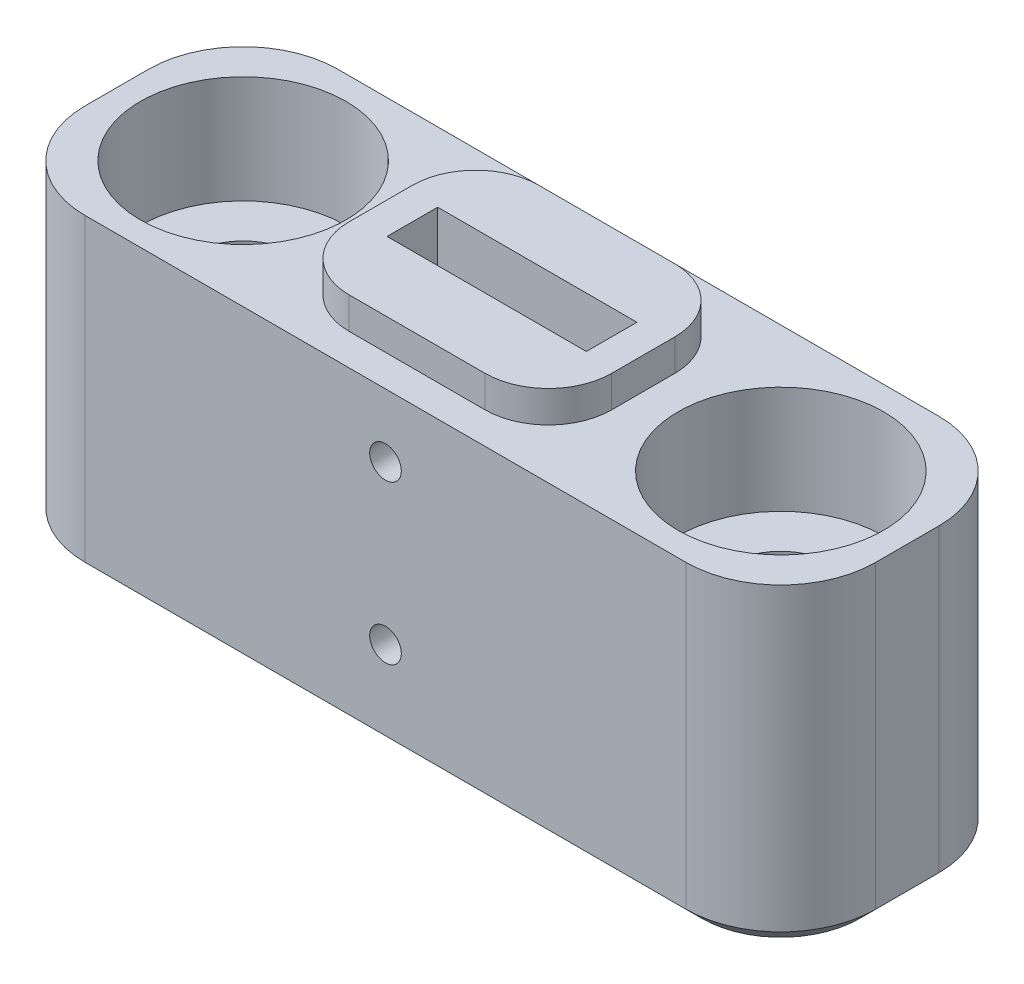
SolidWorks part; units mm, degrees
material "PUR"
ref_plane "Ebene vorne" through (0, 0, 0) normal (0, 0, 1) x (1, 0, 0)
ref_plane "Ebene oben" through (0, 0, 0) normal (0, 1, 0) x (1, 0, 0)
ref_plane "Ebene rechts" through (0, 0, 0) normal (1, 0, 0) x (0, 0, -1)
sketch "Skizze1" plane through (0, 0, 0) normal (0, 0, 1) x (1, 0, 0)
  line L1 (12.5, -5) -> (-12.5, -5)
  line L2 (12.5, -5) -> (12.5, 5)
  line L3 (12.5, 5) -> (-12.5, 5)
  line L4 (-12.5, -5) -> (-12.5, 5)
  line L5 (12.5, -5) -> (-12.5, 5) construction
  line L6 (12.5, 5) -> (-12.5, -5) construction
  point P0 (0, 0)
  dimension "D1" = 10
  dimension "D2" = 25
extrude "Aufsatz-Linear austragen1" add sketch "Skizze1" along normal mid plane 8
hole_wizard "Stirnsenkung für M3 Zylinderschraube mit Innensechskant1" positions "Skizze2" profile "Skizze3" counterbore size "M3" standard "ISO" end condition through all
sketch "Skizze2" plane through (0, 5, 0) normal (0, 1, 0) x (1, 0, 0)
  line L0 (8.5, 0) -> (0, 0) construction
  line L1 (0, 0) -> (-8.5, 0) construction
  point P0 (-8.5, 0)
  point P2 (8.5, 0)
  dimension "D1" = 17
sketch "Skizze3" plane through (-8.5, 5, 0) normal (1, 0, 0) x (0, 0, 1)
  line L0 (0, 0) -> (0, 10)
  line L1 (0, 10) -> (1.7, 10)
  line L3 (1.7, 10) -> (1.7, 3.4)
  line L4 (1.7, 3.4) -> (3.25, 3.4)
  line L5 (3.25, 3.4) -> (3.25, 0)
  line L7 (3.25, 0) -> (0, 0)
  line L11 (0, -6.35) -> (0, 107.95) construction
  dimension "Bohrerdurchmesser" = 3.4
  dimension "Bohrungstiefe" = 10
  dimension "Senkdurchmesser2" = 6.5
  dimension "Senktiefe2" = 3.4
fillet "Verrundung1" radius 3 4 edges at (12.5, 0, -4) (12.5, 0, 4) (-12.5, 0, -4) (-12.5, 0, 4)
sketch "Skizze4" plane through (0, 5, 0) normal (0, 1, 0) x (1, 0, 0)
  line L1 (3.15, -0.8) -> (-3.15, -0.8)
  line L2 (3.15, -0.8) -> (3.15, 0.8)
  line L3 (3.15, 0.8) -> (-3.15, 0.8)
  line L4 (-3.15, -0.8) -> (-3.15, 0.8)
  line L5 (3.15, -0.8) -> (-3.15, 0.8) construction
  line L6 (3.15, 0.8) -> (-3.15, -0.8) construction
  point P0 (0, 0)
  dimension "D1" = 6.3
  dimension "D2" = 1.6
extrude "Schnitt-Linear austragen1" cut sketch "Skizze4" against normal offset from surface (8 mm away) 2 up to face at (-8.5, -5, 1.7)
sketch "Skizze5" plane through (0, 5, 0) normal (0, 1, 0) x (1, 0, 0)
  line L1 (4.15, -3) -> (-4.15, -3)
  line L2 (4.15, -3) -> (4.15, 3)
  line L3 (4.15, 3) -> (-4.15, 3)
  line L4 (-4.15, -3) -> (-4.15, 3)
  line L5 (4.15, -3) -> (-4.15, 3) construction
  line L6 (4.15, 3) -> (-4.15, -3) construction
  line L7 (-3.15, 0.8) -> (-3.15, -0.8) construction
  line L8 (3.15, 0.8) -> (3.15, -0.8) construction
  line L9 (-3.15, -0.8) -> (3.15, -0.8) construction
  line L10 (-3.15, 0.8) -> (3.15, 0.8) construction
  line L11 (3.15, 0.8) -> (3.15, -0.8)
  line L12 (-3.15, -0.8) -> (3.15, -0.8)
  line L13 (-3.15, 0.8) -> (3.15, 0.8)
  line L14 (-3.15, 0.8) -> (-3.15, -0.8)
  line L15 (9.5, 4) -> (-9.5, 4) construction
  point P0 (0, 0)
  dimension "D1" = 1
  dimension "D2" = 1
extrude "Aufsatz-Linear austragen2" add sketch "Skizze5" along normal blind 1
fillet "Verrundung2" radius 2 4 edges at (-4.15, 5.5, -3) (4.15, 5.5, -3) (4.15, 5.5, 3) (-4.15, 5.5, 3)
sketch "Skizze6" plane through (0, 0, 4) normal (0, 0, 1) x (1, 0, 0)
  line L0 (0, 3) -> (0, 0) construction
  line L1 (0, 0) -> (0, -2) construction
  line L2 (-2.15, 6) -> (2.15, 6) construction
  circle A0 centre (0, 3) radius 0.5
  circle A1 centre (0, -2) radius 0.5
  dimension "D1" = 1
  dimension "D2" = 3
  dimension "D3" = 5
extrude "Schnitt-Linear austragen2" cut sketch "Skizze6" against normal through all
chamfer "Fase1" distance 0.5 angle 45 8 edges at (0, -5, -4) (-11.6213, -5, -3.1213) (11.6213, -5, -3.1213) (-12.5, -5, 0) (12.5, -5, 0) (-11.6213, -5, 3.1213) (11.6213, -5, 3.1213) (0, -5, 4)
